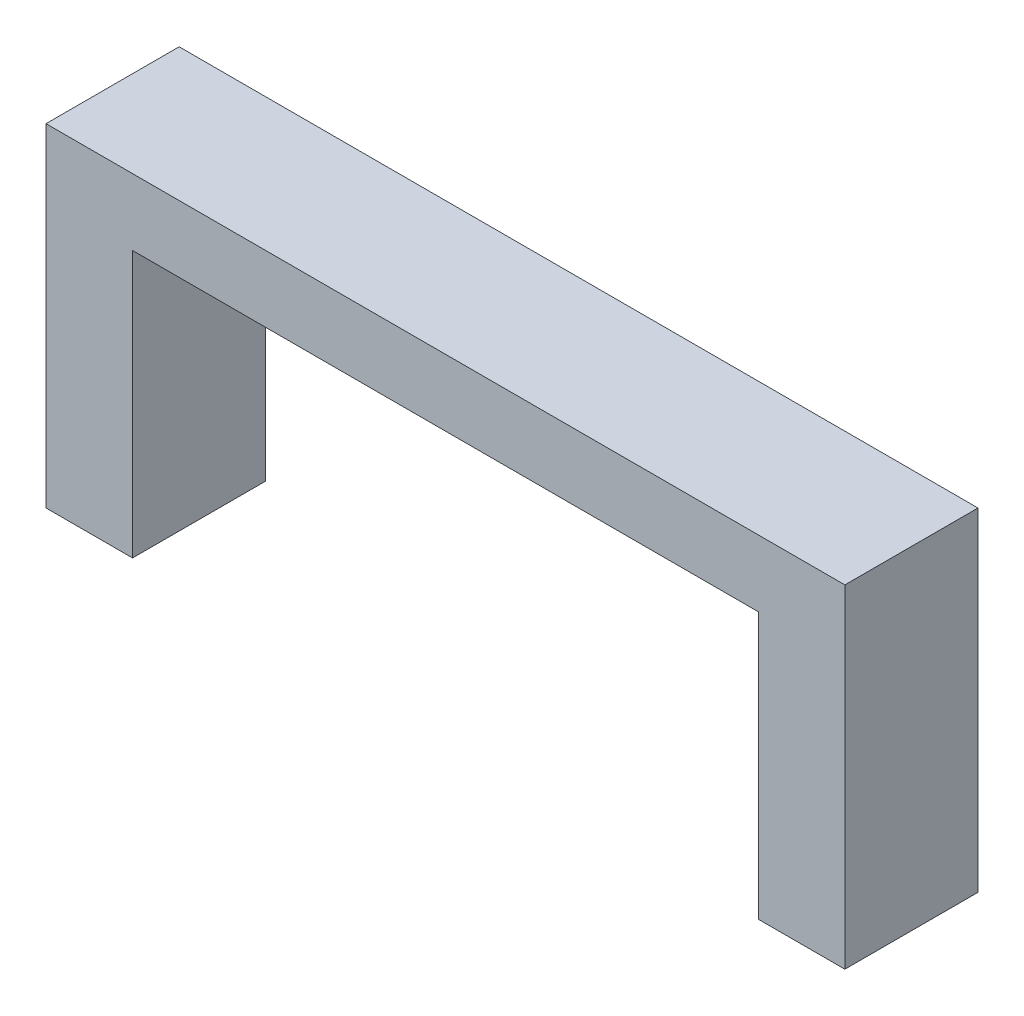
SolidWorks part; units mm, degrees
ref_plane "Front Plane" through (0, 0, 0) normal (0, 0, 1) x (1, 0, 0)
ref_plane "Top Plane" through (0, 0, 0) normal (0, 1, 0) x (1, 0, 0)
ref_plane "Right Plane" through (0, 0, 0) normal (1, 0, 0) x (0, 0, -1)
sketch "Sketch1" plane through (0, 0, 0) normal (0, 0, 1) x (1, 0, 0)
  line L0 (-30, 5) -> (30, 5)
  line L1 (30, 5) -> (30, -20)
  line L2 (30, -20) -> (23.5, -20)
  line L3 (23.5, -20) -> (23.5, 0)
  line L4 (23.5, 0) -> (-23.5, 0)
  line L5 (-23.5, 0) -> (-23.5, -20)
  line L6 (-23.5, -20) -> (-30, -20)
  line L7 (-30, -20) -> (-30, 5)
  point P2 (0, 0)
  dimension "D1" = 6.5
  dimension "D2" = 47
  dimension "D3" = 5
  dimension "D4" = 20
extrude "Boss-Extrude1" add sketch "Sketch1" along normal blind 10
